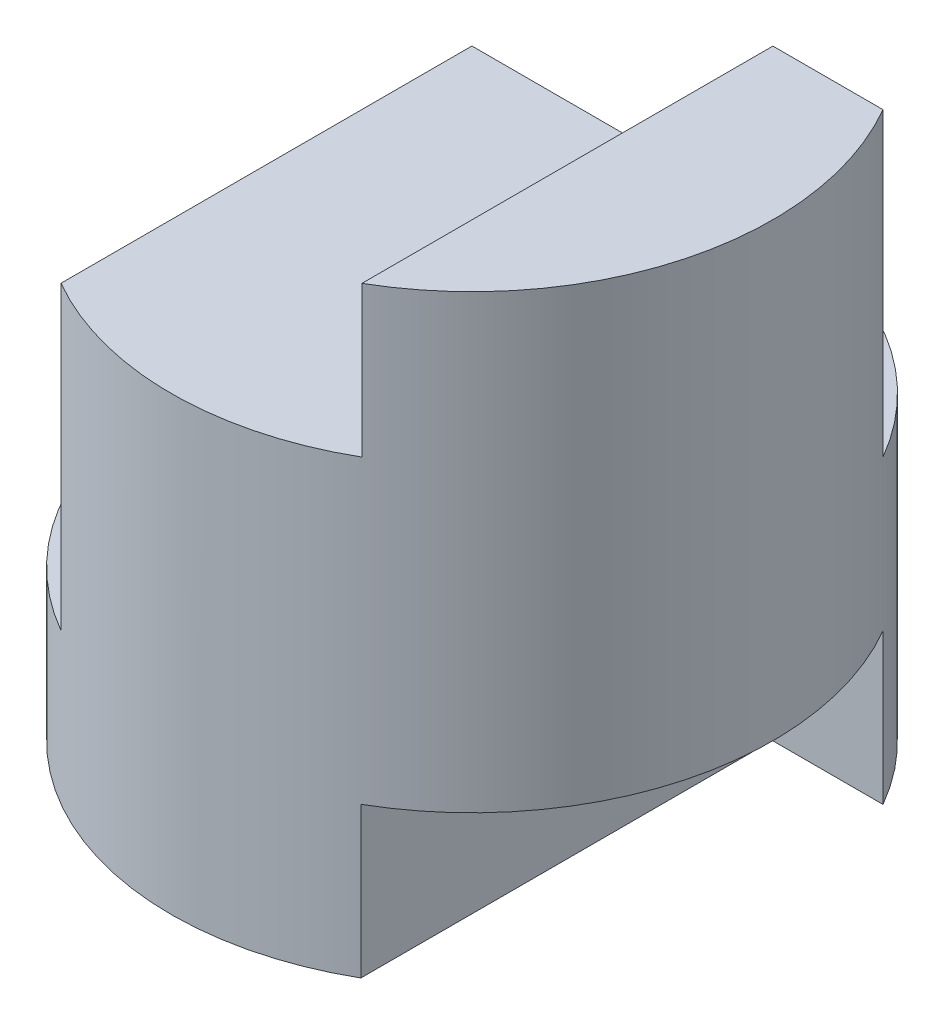
SolidWorks part; units mm, degrees
ref_plane "Front" through (0, 0, 0) normal (0, 0, 1) x (1, 0, 0)
ref_plane "Top" through (0, 0, 0) normal (0, 1, 0) x (1, 0, 0)
ref_plane "Right" through (0, 0, 0) normal (1, 0, 0) x (0, 0, -1)
sketch "Sketch1" plane through (0, 0, 0) normal (0, 1, 0) x (1, 0, 0)
  circle A0 centre (0, 0) radius 2
  dimension "D1" = 4
extrude "Boss-Extrude1" add sketch "Sketch1" along normal blind 4
sketch "Sketch2" plane through (0, 0, 0) normal (0, 0, 1) x (1, 0, 0)
  line L0 (1, 4) -> (-2, 4)
  line L18 (-2, 4) -> (-2, 2)
  line L19 (-2, 4) -> (-2, 0) construction
  line L20 (-2, 2) -> (-1.0009, 2)
  line L21 (-1.0009, 2) -> (-1.0009, 3)
  line L22 (-1.0009, 3) -> (1, 3)
  line L23 (1, 3) -> (1, 4)
  dimension "D1" = 2.0009
  dimension "D2" = 0.9991
extrude "Cut-Extrude1" cut sketch "Sketch2" against normal mid plane 4
sketch "Sketch3" plane through (0, 4, 0) normal (0, 1, 0) x (1, 0, 0)
  line L0 (-1.7321, 1) -> (1.7321, 1)
  arc A0 (-1.0009, 1.7315) -> (-1.0009, -1.7315) centre (0, 0) ccw construction
  arc A1 (1, -1.7321) -> (1, 1.7321) centre (0, 0) ccw construction
  arc A2 (-1.7321, 1) -> (1.7321, 1) centre (0, 0) cw
  dimension "D1" = 1
extrude "Cut-Extrude2" cut sketch "Sketch3" against normal blind 2
sketch "Sketch4" plane through (0, 0, 0) normal (0, 0, 1) x (1, 0, 0)
  line L0 (-2, 2) -> (-2, 0) construction
  line L1 (-1.0009, 2) -> (-2, 2)
  line L2 (-1.0009, 2) -> (-1.0009, 1)
  line L3 (-1.0009, 1) -> (-2, 1)
  line L4 (-2, 2) -> (-2, 1)
  line L6 (2, 0) -> (0.9955, 0)
  line L7 (2, 0) -> (2, 1)
  line L8 (2, 1) -> (0.9955, 1)
  line L9 (0.9955, 0) -> (0.9955, 1)
extrude "Cut-Extrude3" cut sketch "Sketch4" against normal blind 1 and the other way blind 2
